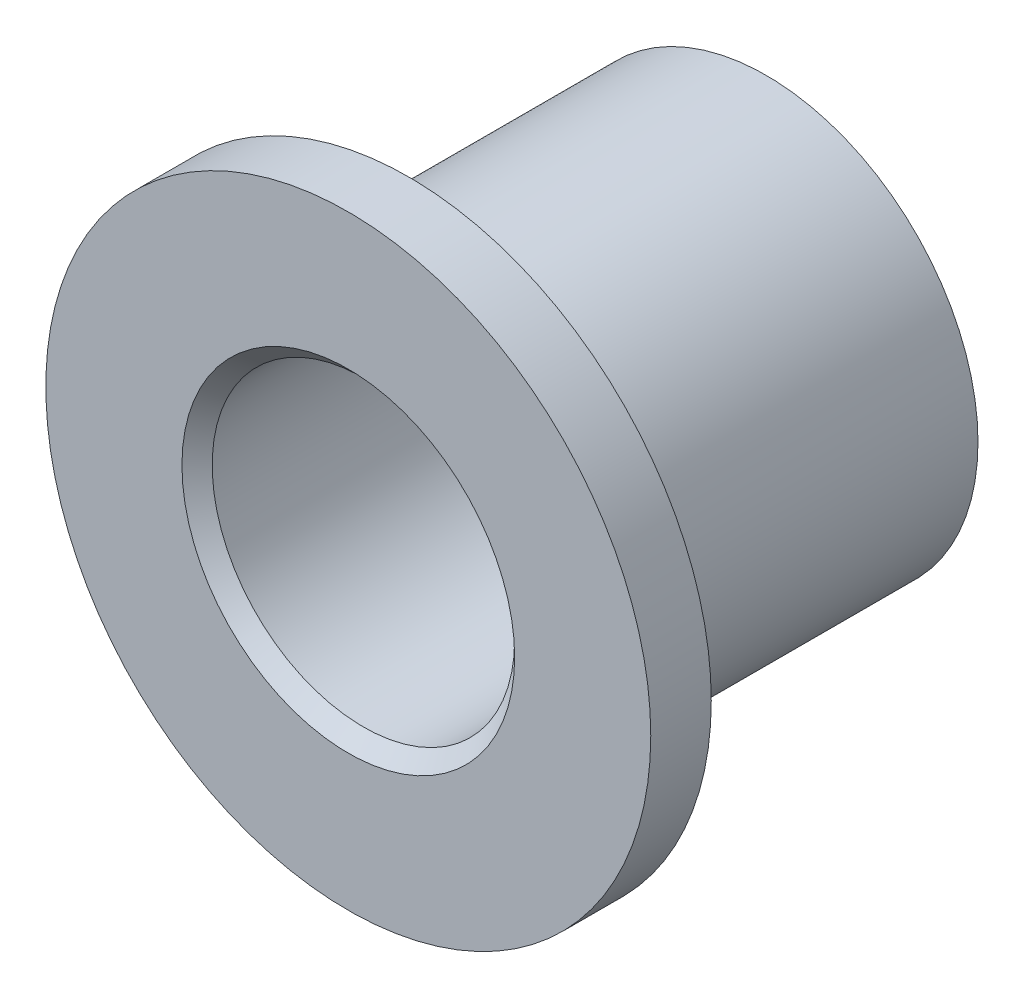
SolidWorks part; units mm, degrees
material "Бронза с оловом"
ref_plane "Спереди" through (0, 0, 0) normal (0, 0, 1) x (1, 0, 0)
ref_plane "Сверху" through (0, 0, 0) normal (0, 1, 0) x (1, 0, 0)
ref_plane "Справа" through (0, 0, 0) normal (1, 0, 0) x (0, 0, -1)
sketch "Эскиз4" plane through (0, 0, 0) normal (0, 0, 1) x (1, 0, 0)
  circle A0 centre (0, 0) radius 3.5
  dimension "D1" = 7
extrude "Бобышка-Вытянуть1" add sketch "Эскиз4" along normal blind 6
sketch "Эскиз5" plane through (0, 0, 6) normal (0, 0, 1) x (1, 0, 0)
  circle A0 centre (0, 0) radius 5
  dimension "D1" = 10
extrude "Бобышка-Вытянуть2" add sketch "Эскиз5" along normal blind 1 contours A0
sketch "Эскиз6" plane through (0, 0, 7) normal (0, 0, 1) x (1, 0, 0)
  circle A0 centre (0, 0) radius 2.5
  dimension "D1" = 5
extrude "Вырез-Вытянуть1" cut sketch "Эскиз6" against normal through all
fillet "Скругление1" radius 0.4 1 edges at (3.5, 0, 6)
chamfer "Фаска1" distance 0.25 angle 20 1 edges at (3.5, 0, 0)
chamfer "Фаска2" distance 0.25 angle 45 1 edges at (2.5, 0, 0)
chamfer "Фаска3" distance 0.25 angle 45 1 edges at (2.5, 0, 7)
